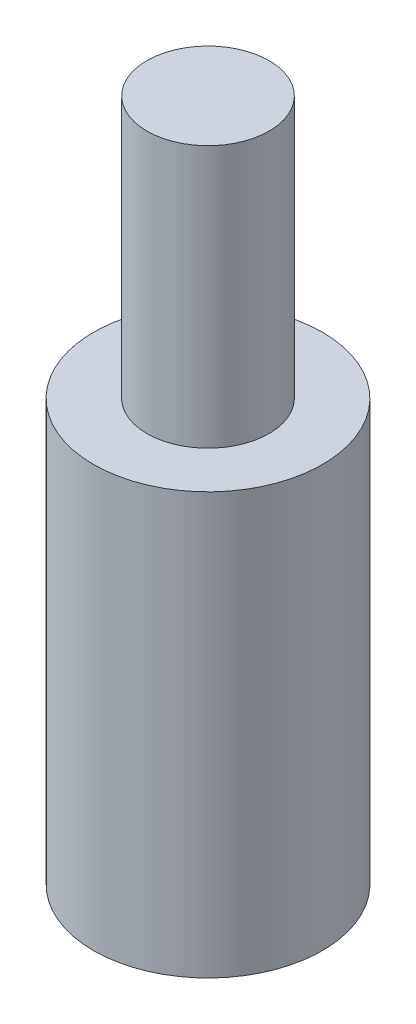
SolidWorks part; units mm, degrees
ref_plane "Спереди" through (0, 0, 0) normal (0, 0, 1) x (1, 0, 0)
ref_plane "Сверху" through (0, 0, 0) normal (0, 1, 0) x (1, 0, 0)
ref_plane "Справа" through (0, 0, 0) normal (1, 0, 0) x (0, 0, -1)
sketch "Эскиз1" plane through (0, 0, 0) normal (0, 0, 1) x (1, 0, 0)
  line L0 (0, 0) -> (-7.5, 0)
  line L1 (-7.5, 0) -> (-7.5, 27.5785)
  line L2 (-7.5, 27.5785) -> (-4, 27.5785)
  line L3 (-4, 27.5785) -> (-4, 44.7384)
  line L4 (-4, 44.7384) -> (0, 44.7384)
  line L5 (0, 44.7384) -> (0, 0)
  line L6 (0, 55.9449) -> (0, -20.9246) construction
  point P9 (0, 0)
revolve "Повернуть1" add sketch "Эскиз1" angle 360 about L6
